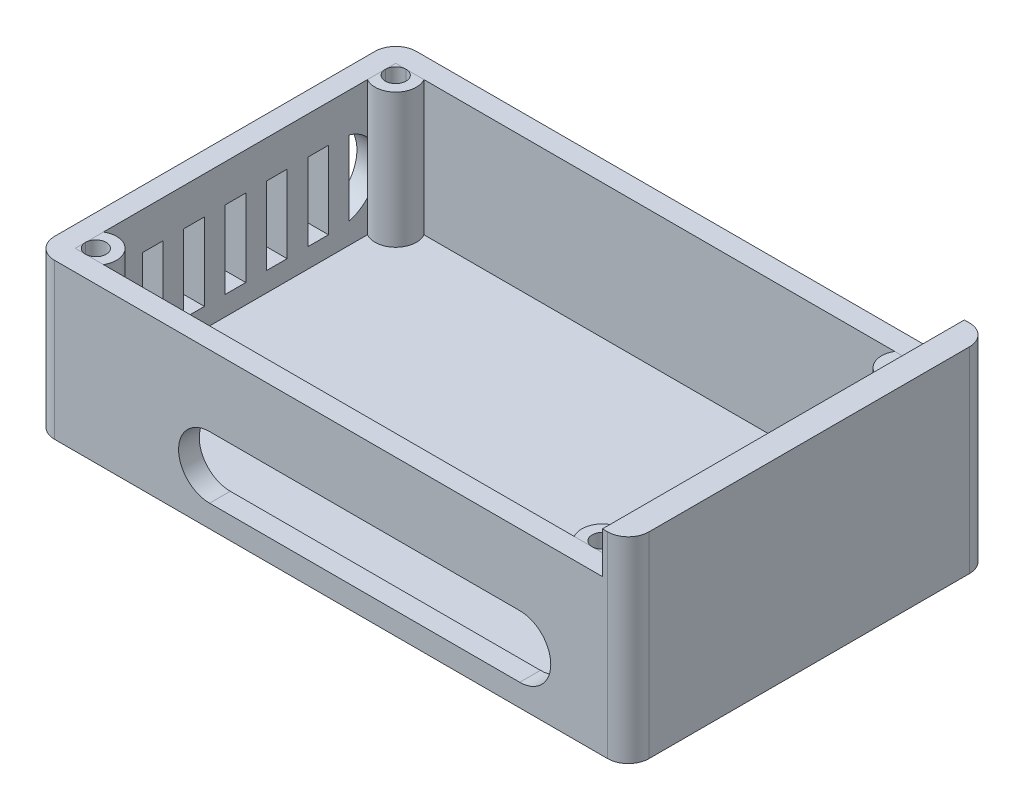
SolidWorks part; units mm, degrees
ref_plane "Front Plane" through (0, 0, 0) normal (0, 0, 1) x (1, 0, 0)
ref_plane "Top Plane" through (0, 0, 0) normal (0, 1, 0) x (1, 0, 0)
ref_plane "Right Plane" through (0, 0, 0) normal (1, 0, 0) x (0, 0, -1)
sketch "Sketch1" plane through (0, 0, 0) normal (0, 1, 0) x (1, 0, 0)
  line L1 (-86.1327, 51.1953) -> (53.5673, 51.1953)
  line L2 (-86.1327, 51.1953) -> (-86.1327, -37.7047)
  line L3 (-86.1327, -37.7047) -> (53.5673, -37.7047)
  line L4 (53.5673, 51.1953) -> (53.5673, -37.7047)
  dimension "D1" = 88.9
  dimension "D2" = 139.7
extrude "Boss-Extrude1" add sketch "Sketch1" along normal blind 38.1
shell "Shell1" thickness 5.08
sketch "Sketch2" plane through (-86.1327, 0, 0) normal (-1, 0, 0) x (0, 0, 1)
  line L0 (-32.1453, 19.3905) -> (18.6547, 19.3905) construction
  line L1 (-32.1453, 28.9155) -> (18.6547, 28.9155)
  line L2 (-32.1453, 9.8655) -> (18.6547, 9.8655)
  line L3 (-32.1453, 19.3905) -> (18.6547, 19.3905) construction
  line L4 (-51.1953, 0) -> (37.7047, 0)
  line L5 (37.7047, 0) -> (37.7047, 38.1)
  line L6 (37.7047, 38.1) -> (-51.1953, 38.1)
  line L7 (-51.1953, 38.1) -> (-51.1953, 0)
  line L8 (-51.1953, 0) -> (37.7047, 0)
  line L9 (37.7047, 0) -> (37.7047, 38.1)
  line L10 (37.7047, 38.1) -> (-51.1953, 38.1)
  line L11 (-51.1953, 38.1) -> (-51.1953, 0)
  line L12 (-19.4453, 6.8655) -> (-19.4453, 31.9155)
  line L13 (-34.6853, 6.8655) -> (-29.6053, 6.8655)
  line L14 (-34.6853, 6.8655) -> (-34.6853, 31.9155)
  line L15 (-34.6853, 31.9155) -> (-29.6053, 31.9155)
  line L16 (-29.6053, 6.8655) -> (-29.6053, 31.9155)
  line L17 (-34.6853, 6.8655) -> (-29.6053, 31.9155) construction
  line L18 (-34.6853, 31.9155) -> (-29.6053, 6.8655) construction
  line L19 (-24.5253, 6.8655) -> (-19.4453, 6.8655)
  line L20 (-24.5253, 6.8655) -> (-24.5253, 31.9155)
  line L21 (-24.5253, 31.9155) -> (-19.4453, 31.9155)
  line L22 (-9.2853, 6.8655) -> (-9.2853, 31.9155)
  line L23 (-14.3653, 6.8655) -> (-9.2853, 6.8655)
  line L24 (-14.3653, 6.8655) -> (-14.3653, 31.9155)
  line L25 (-14.3653, 31.9155) -> (-9.2853, 31.9155)
  line L26 (0.8747, 6.8655) -> (0.8747, 31.9155)
  line L27 (-4.2053, 6.8655) -> (0.8747, 6.8655)
  line L28 (-4.2053, 6.8655) -> (-4.2053, 31.9155)
  line L29 (-4.2053, 31.9155) -> (0.8747, 31.9155)
  line L30 (11.0347, 6.8655) -> (11.0347, 31.9155)
  line L31 (5.9547, 6.8655) -> (11.0347, 6.8655)
  line L32 (5.9547, 6.8655) -> (5.9547, 31.9155)
  line L33 (5.9547, 31.9155) -> (11.0347, 31.9155)
  line L34 (21.1947, 6.8655) -> (21.1947, 31.9155)
  line L35 (16.1147, 6.8655) -> (21.1947, 6.8655)
  line L36 (16.1147, 6.8655) -> (16.1147, 31.9155)
  line L37 (16.1147, 31.9155) -> (21.1947, 31.9155)
  arc A0 (-32.1453, 28.9155) -> (-32.1453, 9.8655) centre (-32.1453, 19.3905) ccw
  arc A1 (18.6547, 9.8655) -> (18.6547, 28.9155) centre (18.6547, 19.3905) ccw
  point P6 (-6.7453, 19.3905)
  dimension "D2" = 50.8
  dimension "D3" = 19.05
  dimension "D4" = 19.05
  dimension "D5" = 18.7095
  dimension "D6" = 5.08
  dimension "D1" = 0
  dimension "D7" = 6
extrude "Cut-Extrude1" cut sketch "Sketch2" against normal blind 5.08 contours L14 A0 | L2 L20 L1 L16 | L2 L24 L1 L12 | L2 L28 L1 L22 | L2 L32 L1 L26 | L2 L36 L1 L30 | L34 A1
sketch "Sketch3" plane through (0, 0, 37.7047) normal (0, 0, 1) x (1, 0, 0)
  line L0 (33.2473, 13.081) -> (-42.9527, 13.081) construction
  line L1 (33.2473, 5.461) -> (-42.9527, 5.461)
  line L2 (33.2473, 20.701) -> (-42.9527, 20.701)
  line L3 (53.5673, 38.1) -> (53.5673, 0) construction
  line L4 (-86.1327, 0) -> (53.5673, 0) construction
  arc A0 (33.2473, 5.461) -> (33.2473, 20.701) centre (33.2473, 13.081) ccw
  arc A1 (-42.9527, 20.701) -> (-42.9527, 5.461) centre (-42.9527, 13.081) ccw
  point P2 (-4.8527, 13.081)
  point P7 (40.8673, 13.081)
  dimension "D1" = 76.2
  dimension "D2" = 12.7
  dimension "D3" = 15.24
  dimension "D5" = 5.461
extrude "Cut-Extrude2" cut sketch "Sketch3" against normal blind 5.08
sketch "Sketch4" plane through (0, 38.1, 0) normal (0, 1, 0) x (1, 0, 0)
  line L0 (48.4873, 46.1153) -> (-81.0527, 46.1153) construction
  line L1 (-81.0527, 46.1153) -> (-81.0527, -32.6247) construction
  line L2 (48.4873, 46.1153) -> (-81.0527, 46.1153) construction
  line L3 (48.4873, -32.6247) -> (48.4873, 46.1153) construction
  line L4 (-81.0527, -32.6247) -> (48.4873, -32.6247) construction
  line L5 (-81.0527, -32.6247) -> (48.4873, -32.6247) construction
  line L6 (-81.0527, 46.1153) -> (-81.0527, -32.6247) construction
  line L11 (-86.1327, 51.1953) -> (-86.1327, -37.7047)
  line L12 (-86.1327, -37.7047) -> (53.5673, -37.7047)
  line L13 (53.5673, -37.7047) -> (53.5673, 51.1953)
  line L14 (53.5673, 51.1953) -> (-86.1327, 51.1953)
  line L15 (-86.1327, 51.1953) -> (-86.1327, -37.7047)
  line L16 (-86.1327, -37.7047) -> (53.5673, -37.7047)
  line L17 (53.5673, -37.7047) -> (53.5673, 51.1953)
  line L18 (53.5673, 51.1953) -> (-86.1327, 51.1953)
  circle A0 centre (-78.5127, 43.5753) radius 2.54
  circle A1 centre (45.9473, 43.5753) radius 2.54
  circle A2 centre (-78.5127, -30.0847) radius 2.54
  circle A3 centre (45.9473, -30.0847) radius 2.54
  circle A4 centre (-78.5127, 43.5753) radius 5.08
  circle A5 centre (-78.5127, -30.0847) radius 5.08
  circle A6 centre (45.9473, -30.0847) radius 5.08
  circle A7 centre (45.9473, 43.5753) radius 5.08
  line M5 (-81.0527, -32.6247) -> (-81.0527, 46.1153)
  line M6 (-81.0527, 46.1153) -> (48.4873, 46.1153)
  line M7 (48.4873, 46.1153) -> (48.4873, -32.6247)
  line M8 (48.4873, -32.6247) -> (-81.0527, -32.6247)
  dimension "D1" = 5.08
  dimension "D2" = 5.08
  dimension "D3" = 5.08
  dimension "D4" = 5.08
  dimension "D5" = 2.54
  dimension "D6" = 2.54
  dimension "D8" = 2.54
  dimension "D9" = 2.54
  dimension "D10" = 2.54
  dimension "D11" = 2.54
  dimension "D12" = 2.54
  dimension "D13" = 2.54
  dimension "D7" = 2.54
  dimension "D14" = 2.54
  dimension "D15" = 0
extrude "Boss-Extrude2" add sketch "Sketch4" against normal blind 33.02 separate body contours A1 M7 M6 | A7 A1 M6 M7 | A3 M8 M7 | A6 A3 M7 M8 | A2 M5 M8 | A5 A2 M8 M5 | A0 M6 M5 | A4 A0 M5 M6
sketch "Sketch5" plane through (0, 38.1, 0) normal (0, 1, 0) x (1, 0, 0)
  line L1 (53.5673, -37.7047) -> (59.9173, -37.7047)
  line L2 (53.5673, -37.7047) -> (53.5673, 51.1953)
  line L3 (53.5673, 51.1953) -> (59.9173, 51.1953)
  line L4 (59.9173, -37.7047) -> (59.9173, 51.1953)
  dimension "D1" = 88.9
  dimension "D2" = 6.35
extrude "Boss-Extrude3" add sketch "Sketch5" against normal blind 38.1
sketch "Sketch6" plane through (0, 38.1, 0) normal (0, 1, 0) x (1, 0, 0)
  line L0 (-86.1327, -37.7047) -> (59.9173, -37.7047) construction
  line L1 (59.9173, 51.1953) -> (53.5673, 51.1953)
  line L2 (59.9173, 51.1953) -> (59.9173, -37.7047)
  line L3 (59.9173, -37.7047) -> (53.5673, -37.7047)
  line L4 (53.5673, 51.1953) -> (53.5673, -37.7047)
  dimension "D1" = 6.35
  dimension "D2" = 88.9
extrude "Boss-Extrude4" add sketch "Sketch6" along normal blind 10.16
fillet "Fillet1" radius 5.08 4 edges at (59.9173, 24.13, -51.1953) (-86.1327, 19.05, -51.1953) (-86.1327, 19.05, 37.7047) (59.9173, 24.13, 37.7047)
